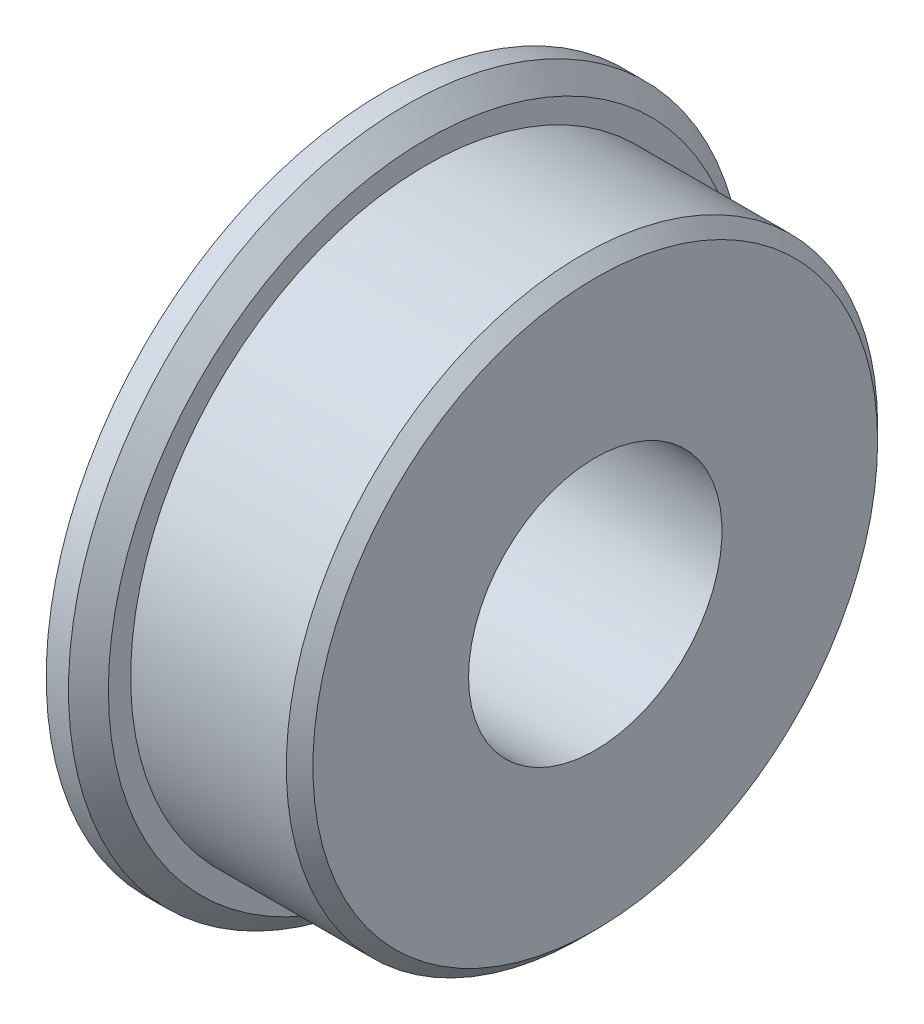
SolidWorks part; units mm, degrees
material "6061-T6 (SS)"
ref_plane "Front Plane" through (0, 0, 0) normal (0, 0, 1) x (1, 0, 0)
ref_plane "Top Plane" through (0, 0, 0) normal (0, 1, 0) x (1, 0, 0)
ref_plane "Right Plane" through (0, 0, 0) normal (1, 0, 0) x (0, 0, -1)
sketch "Sketch1" plane through (0, 0, 0) normal (1, 0, 0) x (0, 0, -1)
  circle A0 centre (0, 0) radius 25.4
  dimension "D1" = 50.8
extrude "Boss-Extrude1" add sketch "Sketch1" along normal blind 3.175
sketch "Sketch2" plane through (3.175, 0, 0) normal (1, 0, 0) x (0, 0, -1)
  circle A0 centre (0, 0) radius 22.225
  circle A1 centre (0, 0) radius 25.4 construction
  dimension "D1" = 3.175
extrude "Boss-Extrude2" add sketch "Sketch2" along normal blind 12.7
sketch "Sketch3" plane through (0, 0, 0) normal (-1, 0, 0) x (0, 0, 1)
  circle A0 centre (0, 0) radius 9.525
  dimension "D1" = 19.05
extrude "Cut-Extrude1" cut sketch "Sketch3" against normal through all
chamfer "Chamfer1" distance 1.5 angle 45 1 edges at (3.175, 0, -25.4)
chamfer "Chamfer2" distance 1 angle 45 1 edges at (15.875, 0, -22.225)
